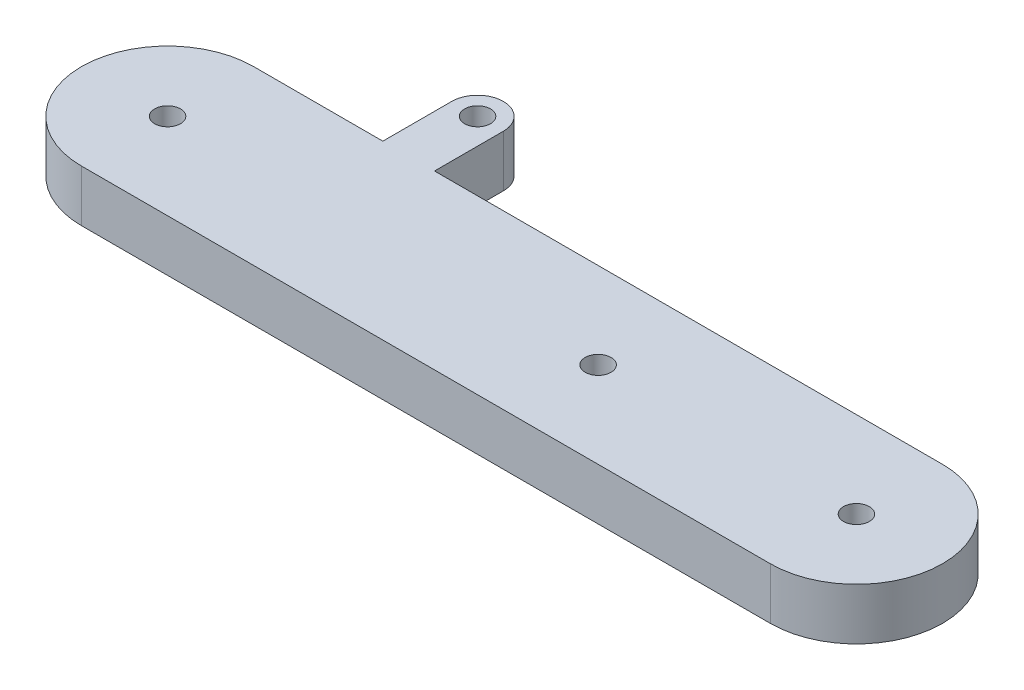
SolidWorks part; units mm, degrees
ref_plane "Front Plane" through (0, 0, 0) normal (0, 0, 1) x (1, 0, 0)
ref_plane "Top Plane" through (0, 0, 0) normal (0, 1, 0) x (1, 0, 0)
ref_plane "Right Plane" through (0, 0, 0) normal (1, 0, 0) x (0, 0, -1)
sketch "Sketch1" plane through (0, 0, 0) normal (0, 1, 0) x (1, 0, 0)
  line L0 (-40, 20) -> (-40, 0) construction
  line L1 (0, 0) -> (-80, 0)
  line L3 (0, 20) -> (-59, 20)
  line L6 (-59, 20) -> (-59, 28)
  line L8 (-65, 20) -> (-65, 28)
  line L9 (-65, 20) -> (-80, 20)
  arc A0 (-80, 20) -> (-80, 0) centre (-80, 10) ccw
  arc A1 (0, 20) -> (0, 0) centre (0, 10) cw
  circle A2 centre (-80, 10) radius 1.5
  circle A3 centre (0, 10) radius 1.5
  circle A4 centre (-30, 10) radius 1.5
  arc A5 (-59, 28) -> (-65, 28) centre (-62, 28) ccw
  circle A6 centre (-62, 28) radius 1.5
  dimension "D3" = 20
  dimension "D4" = 3
  dimension "D5" = 3
  dimension "D10" = 6
  dimension "D11" = 3
  dimension "D1" = 80
  dimension "D2" = 20
  dimension "D6" = 30
  dimension "D7" = 15
  dimension "D8" = 6
  dimension "D9" = 8
extrude "Boss-Extrude1" add sketch "Sketch1" along normal blind 6
